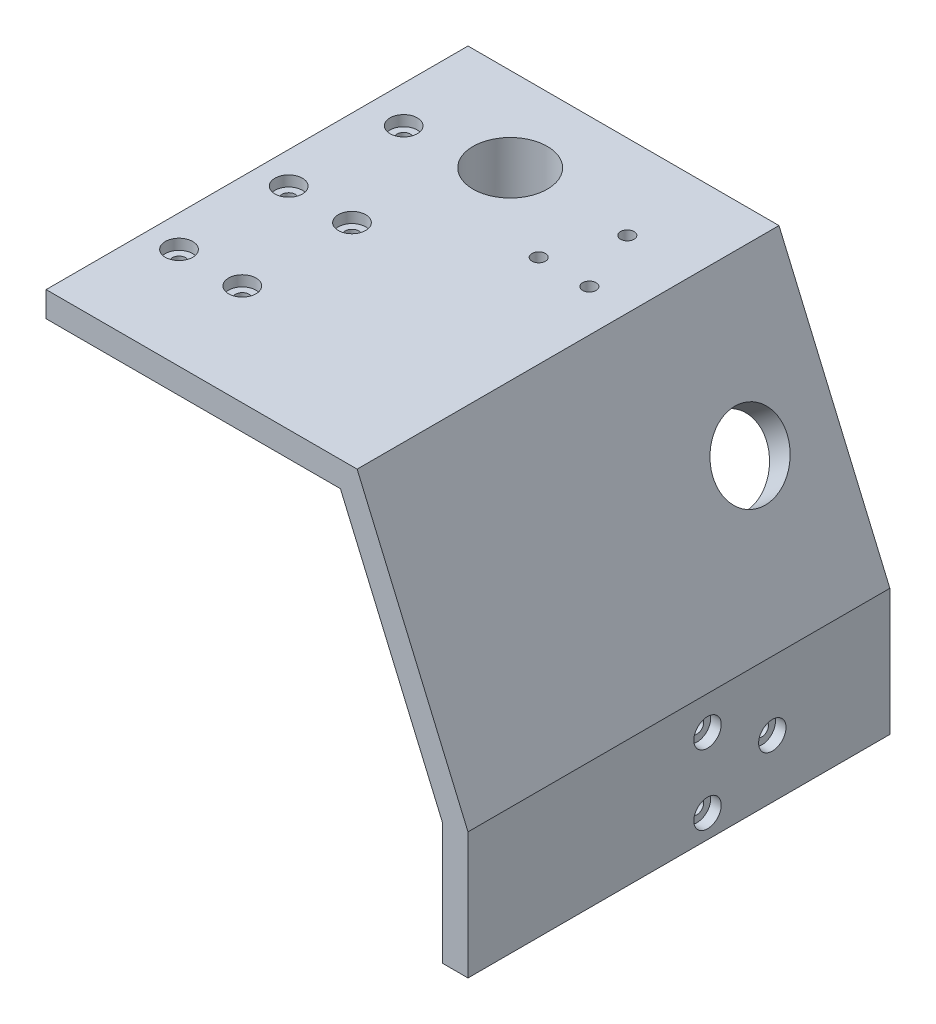
SolidWorks part; units mm, degrees
ref_plane "Alzado" through (0, 0, 0) normal (0, 0, 1) x (1, 0, 0)
ref_plane "Planta" through (0, 0, 0) normal (0, 1, 0) x (1, 0, 0)
ref_plane "Vista lateral" through (0, 0, 0) normal (1, 0, 0) x (0, 0, -1)
sketch "Croquis1" plane through (0, 0, 0) normal (0, 0, 1) x (1, 0, 0)
  line L1 (-100, 25) -> (-73.7179, 86.3249) construction
  line L2 (-73.7179, 86.3249) -> (73.7179, 86.3249) construction
  line L3 (100, 25) -> (100, -5) construction
  line L4 (100, 25) -> (73.7179, 86.3249) construction
  line L5 (-100, 25) -> (-100, -5)
  line L6 (-100, 25) -> (-73.7179, 86.3249)
  line L7 (-73.7179, 86.3249) -> (73.7179, 86.3249)
  line L8 (100, 25) -> (100, -5)
  line L9 (100, 25) -> (73.7179, 86.3249)
  line L10 (-94, 23.7685) -> (-94, -5)
  line L11 (-94, 23.7685) -> (-69.7615, 80.3249)
  line L12 (-69.7615, 80.3249) -> (69.7615, 80.3249)
  line L13 (94, 23.7685) -> (69.7615, 80.3249)
  line L14 (94, 23.7685) -> (94, -5)
  line L15 (-94, -5) -> (-100, -5)
  line L16 (100, -5) -> (94, -5)
  dimension "D2" = 30
  dimension "D1" = 6
extrude "Saliente-Extruir1" add sketch "Croquis1" along normal blind 100
sketch "Croquis3" plane through (0, 86.3249, 0) normal (0, 1, 0) x (1, 0, 0)
  line L0 (73.7179, 0) -> (-73.7179, 0) construction
  line L1 (73.7179, -100) -> (73.7179, 0) construction
  line L2 (-73.7179, -100) -> (-73.7179, 0) construction
  circle A2 centre (-30, -20) radius 8.8
  circle A3 centre (30, -20) radius 8.8
  dimension "D4" = 17.6
  dimension "D5" = 17.6
  dimension "D1" = 20
  dimension "D2" = 20
  dimension "D3" = 43.7179
  dimension "D6" = 43.7179
extrude "Cortar-Extruir1" cut sketch "Croquis3" against normal up to next
ref_plane "Plano1" through (-87.4795, 68.8361, 0) normal (-0.7859, 0.6184, 0) x (0, 0, -1)
sketch "Croquis4" plane through (-87.4795, 68.8361, 0) normal (-0.7859, 0.6184, 0) x (0, 0, -1)
  line L0 (0, -22.254) -> (0, 42.1921) construction
  line L1 (-100, -22.254) -> (0, -22.254) construction
  line L2 (-100, -22.254) -> (-100, 42.1921) construction
  line L3 (-100, 42.1921) -> (0, 42.1921) construction
  line L4 (0, -22.254) -> (0, 42.1921) construction
  line L5 (-100, -22.254) -> (0, -22.254) construction
  line L6 (-100, -22.254) -> (-100, 42.1921) construction
  line L7 (-100, 42.1921) -> (0, 42.1921) construction
  line L8 (0, 9.9691) -> (-100, 9.9691) construction
  circle A0 centre (-20, 9.9691) radius 8.8
  dimension "D1" = 17.6
  dimension "D2" = 20
extrude "Cortar-Extruir2" cut sketch "Croquis4" against normal up to next
mirror "Simetría1" about plane through (0, 0, 0) normal (1, 0, 0) of "Cortar-Extruir2"
sketch "Croquis5" plane through (0, 80.3249, 0) normal (0, -1, 0) x (1, 0, 0)
  line L0 (15.175, 0) -> (15.175, 2.3)
  line L1 (15.175, 2.3) -> (3.7842, 2.3)
  line L3 (-3.7842, 2.3) -> (-15.175, 2.3)
  line L4 (-15.175, 2.3) -> (-15.175, 0)
  line L10 (-14.875, 0) -> (-3.2619, 0)
  line L11 (3.2619, 0) -> (14.875, 0)
  line L12 (14.875, 0) -> (14.875, 2)
  line L13 (14.875, 2) -> (3.7202, 2)
  line L14 (-3.7202, 2) -> (-14.875, 2)
  line L15 (-14.875, 2) -> (-14.875, 0)
  line L17 (-15.175, 0) -> (3.2619, 0)
  line L19 (-3.2619, 0) -> (15.175, 0)
  line L20 (14.875, 0) -> (14.875, 2)
  line L22 (14.875, 2) -> (3.7202, 2)
  line L23 (-3.7202, 2) -> (-14.875, 2)
  line L24 (-14.875, 2) -> (-14.875, 0)
  arc A0 (3.7842, 2.3) -> (-3.7842, 2.3) centre (0, -6.25) ccw
  arc A3 (3.2619, 0) -> (-3.2619, 0) centre (0, -6.25) ccw
  arc A4 (3.7202, 2) -> (-3.7202, 2) centre (0, -6.25) ccw
  arc A5 (3.2619, 0) -> (-3.2619, 0) centre (0, -6.25) ccw
  arc A7 (3.7202, 2) -> (-3.7202, 2) centre (0, -6.25) ccw
  dimension "D1" = 0
  dimension "D2" = 0.3
extrude "Cortar-Extruir3" cut sketch "Croquis5" against normal blind 0.5
sketch "Croquis6" plane through (-100, 0, 0) normal (-1, 0, 0) x (0, 0, 1)
  circle A0 centre (43.227, 0.4977) radius 1.6 construction
  circle A1 centre (27.8635, 8.7685) radius 1.6 construction
  circle A2 centre (43.227, 17.0392) radius 1.6 construction
  circle A3 centre (43.227, 0.4977) radius 1.6
  circle A4 centre (27.8635, 8.7685) radius 1.6
  circle A5 centre (43.227, 17.0392) radius 1.6
extrude "Cortar-Extruir4" cut sketch "Croquis6" against normal up to next
sketch "Croquis7" plane through (-100, 0, 0) normal (-1, 0, 0) x (0, 0, 1)
  circle A0 centre (27.8635, 8.7685) radius 3.25
  circle A1 centre (43.227, 0.4977) radius 3.25
  circle A2 centre (43.227, 17.0392) radius 3.25
  dimension "D1" = 6.5
extrude "Cortar-Extruir5" cut sketch "Croquis7" against normal blind 2.5
mirror "Simetría2" about plane through (0, 0, 0) normal (1, 0, 0) of "Cortar-Extruir5", "Cortar-Extruir4"
sketch "Croquis8" plane through (0, 80.3249, 0) normal (0, -1, 0) x (1, 0, 0)
  line L0 (0, 100) -> (0, 0) construction
  line L1 (-37.5, 82) -> (37.5, 82)
  line L3 (-37.5, 70) -> (37.5, 70)
  line L5 (-69.7615, 100) -> (69.7615, 100) construction
  line L7 (-37.5, 56) -> (37.5, 56)
  line L8 (-37.5, 56) -> (-37.5, 44)
  line L9 (-37.5, 44) -> (37.5, 44)
  line L10 (37.5, 56) -> (37.5, 44)
  line L11 (-69.7615, 50) -> (69.7615, 50) construction
  line L12 (-69.7615, 100) -> (-69.7615, 0) construction
  line L13 (69.7615, 100) -> (69.7615, 0) construction
  line L14 (-17.5, 30) -> (17.5, 30)
  line L15 (-17.5, 30) -> (-17.5, 18)
  line L16 (-17.5, 18) -> (17.5, 18)
  line L17 (17.5, 30) -> (17.5, 18)
  line L19 (-73.7179, 0) -> (73.7179, 0) construction
  line L20 (-37.5, 76) -> (37.5, 76) construction
  line L21 (-37.5, 70) -> (-37.5, 82)
  line L24 (37.5, 82) -> (37.5, 70)
  point P29 (37.5, 76)
  dimension "D1" = 12
  dimension "D3" = 12
  dimension "D4" = 30
  dimension "D5" = 75
  dimension "D6" = 12
  dimension "D7" = 30
  dimension "D8" = 35
  dimension "D9" = 75
extrude "Cortar-Extruir6" cut sketch "Croquis8" against normal blind 2.5
sketch "Croquis9" plane through (0, 82.8249, 0) normal (0, -1, 0) x (1, 0, 0)
  line L0 (-37.4, 76) -> (37.4, 76) construction
  line L1 (-37.5, 50) -> (37.5, 50) construction
  line L2 (-37.5, 56) -> (-37.5, 44) construction
  line L3 (-37.4, 81.9) -> (-37.4, 70.1) construction
  line L4 (37.5, 44) -> (37.5, 56) construction
  line L5 (-17.5, 24) -> (17.5, 24) construction
  line L6 (37.4, 70.1) -> (37.4, 81.9) construction
  line L7 (-37.5, 82) -> (-37.5, 70) construction
  line L8 (73.7179, 0) -> (-73.7179, 0)
  line L9 (73.7179, -6) -> (73.7179, 0)
  line L10 (-73.7179, -6) -> (73.7179, -6)
  line L11 (-73.7179, 0) -> (-73.7179, -6)
  line L12 (73.7179, 0) -> (-73.7179, 0) construction
  line L14 (0, 100) -> (0, 0) construction
  line L15 (-69.7615, 100) -> (69.7615, 100) construction
  line L23 (-17.5, 30) -> (-17.5, 18) construction
  line L24 (17.5, 18) -> (17.5, 30) construction
  line L25 (-37.5, 56) -> (-37.5, 44) construction
  line L28 (0, 18) -> (-17.5, 30) construction
  line L29 (-17.5, 18) -> (17.5, 18) construction
  line L30 (0, 30) -> (-17.5, 18) construction
  line L31 (17.5, 30) -> (-17.5, 30) construction
  circle A7 centre (-22.5, 76) radius 1.6
  circle A8 centre (-7.5, 76) radius 1.6
  circle A9 centre (7.5, 76) radius 1.6
  circle A10 centre (22.5, 76) radius 1.6
  circle A15 centre (-22.5, 50) radius 1.6
  circle A16 centre (-7.5, 50) radius 1.6
  circle A17 centre (7.5, 50) radius 1.6
  circle A18 centre (22.5, 50) radius 1.6
  circle A19 centre (-8.75, 24) radius 1.6
  circle A21 centre (8.75, 24) radius 1.6
  dimension "D1" = 3.2
  dimension "D2" = 15
  dimension "D3" = 15
  dimension "D4" = 15
  dimension "D7" = 15
  dimension "D11" = 3.2
  dimension "D13" = 3.2
  dimension "D5" = 15
  dimension "D6" = 0
  dimension "D8" = 15
  dimension "D10" = 15
  dimension "D9" = 15
extrude "Cortar-Extruir7" cut sketch "Croquis9" against normal up to next
sketch "Croquis10" plane through (0, 86.3249, 0) normal (0, 1, 0) x (1, 0, 0)
  circle A0 centre (-22.5, -50) radius 3.25
  circle A1 centre (-7.5, -50) radius 3.25
  circle A2 centre (7.5, -50) radius 3.25
  circle A3 centre (22.5, -50) radius 3.25
  circle A4 centre (8.75, -24) radius 3.25
  circle A5 centre (-8.75, -24) radius 3.25
  circle A6 centre (22.5, -50) radius 1.6 construction
  circle A7 centre (7.5, -50) radius 1.6 construction
  circle A8 centre (-7.5, -50) radius 1.6 construction
  circle A9 centre (-22.5, -50) radius 1.6 construction
  circle A10 centre (22.5, -76) radius 3.25
  circle A11 centre (7.5, -76) radius 3.25
  circle A12 centre (-7.5, -76) radius 3.25
  circle A13 centre (-22.5, -76) radius 3.25
  circle A14 centre (-8.75, -24) radius 1.6 construction
  circle A15 centre (8.75, -24) radius 1.6 construction
  dimension "D1" = 6.5
  dimension "D2" = 6.5
  dimension "D3" = 6.5
  dimension "D4" = 6.5
  dimension "D5" = 6.5
extrude "Cortar-Extruir8" cut sketch "Croquis10" against normal blind 2.5
sketch "Croquis11" plane through (0, 80.3249, 0) normal (0, -1, 0) x (1, 0, 0)
  circle A0 centre (30, 20) radius 8.8 construction
  circle A1 centre (-30, 20) radius 8.8 construction
  circle A2 centre (30, 20) radius 8.8
  circle A3 centre (-30, 20) radius 8.8
  circle A4 centre (-30, 20) radius 10.3
  circle A5 centre (30, 20) radius 10.3
  dimension "D1" = 1.5
extrude "Saliente-Extruir2" add sketch "Croquis11" along normal blind 10
ref_plane "Plano2" through (-63.9034, 50.2844, 0) normal (-0.7859, 0.6184, 0) x (0, 0, -1)
sketch "Croquis12" plane through (-63.9034, 50.2844, 0) normal (-0.7859, 0.6184, 0) x (0, 0, -1)
  circle A0 centre (-20, 9.9691) radius 8.8 construction
  circle A1 centre (-20, 9.9691) radius 8.8
  circle A2 centre (-20, 9.9691) radius 10.3
  dimension "D1" = 1.5
extrude "Saliente-Extruir3" add sketch "Croquis12" along normal up to next
sketch "Croquis13" plane through (0, 80.3249, 0) normal (0, -1, 0) x (1, 0, 0)
  circle A0 centre (57.7615, 20) radius 1.6 construction
  circle A1 centre (51.7615, 35) radius 1.6 construction
  circle A2 centre (63.7615, 35) radius 1.6 construction
  circle A3 centre (-57.7615, 20) radius 1.6 construction
  circle A4 centre (-63.7615, 35) radius 1.6 construction
  circle A5 centre (-51.7615, 35) radius 1.6 construction
  circle A6 centre (57.7615, 20) radius 1.6
  circle A7 centre (51.7615, 35) radius 1.6
  circle A8 centre (63.7615, 35) radius 1.6
  circle A9 centre (-57.7615, 20) radius 1.6
  circle A10 centre (-63.7615, 35) radius 1.6
  circle A11 centre (-51.7615, 35) radius 1.6
extrude "Cortar-Extruir9" cut sketch "Croquis13" against normal up to next
sketch "Croquis14" plane through (0, 86.3249, 0) normal (0, 1, 0) x (1, 0, 0)
  line L0 (73.7179, -100) -> (-73.7179, -100) construction
  line L1 (0, -100) -> (-100, -100)
  line L2 (0, -100) -> (0, 0)
  line L3 (0, 0) -> (-100, 0)
  line L4 (-100, -100) -> (-100, 0)
extrude "Cortar-Extruir10" cut sketch "Croquis14" against normal through all
